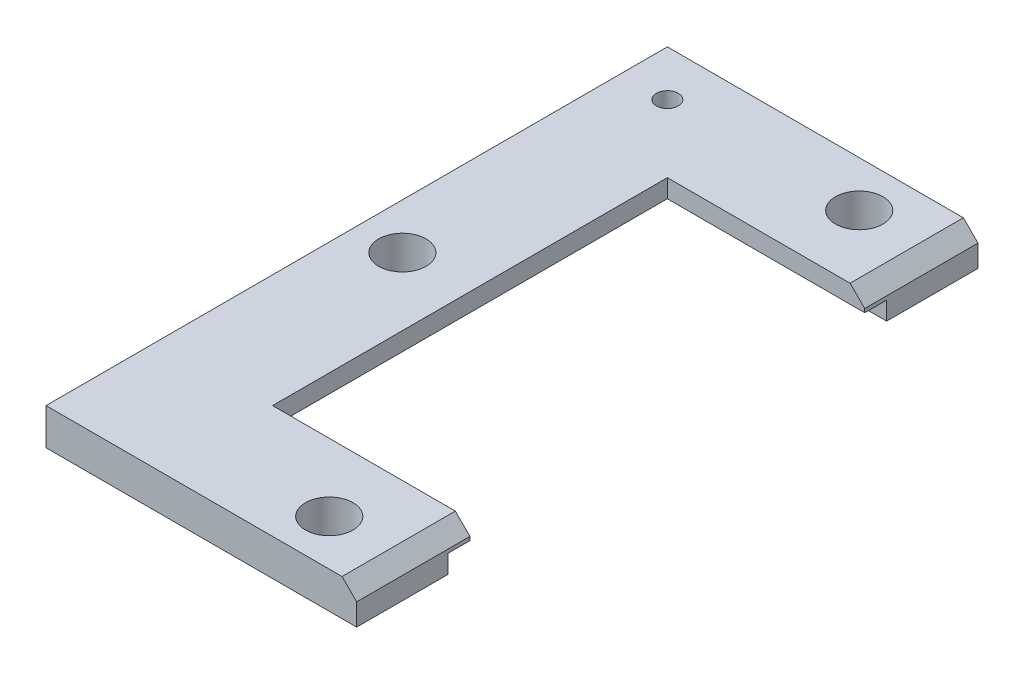
SolidWorks part; units mm, degrees
material "Plain Carbon Steel"
ref_plane "Front Plane" through (0, 0, 0) normal (0, 0, 1) x (1, 0, 0)
ref_plane "Top Plane" through (0, 0, 0) normal (0, 1, 0) x (1, 0, 0)
ref_plane "Right Plane" through (0, 0, 0) normal (1, 0, 0) x (0, 0, -1)
sketch "Sketch1" plane through (0, 0, 0) normal (0, 1, 0) x (1, 0, 0)
  line L0 (-133.1766, -85) -> (-133.1766, -54)
  line L1 (-218.1766, 85) -> (-133.1766, 85)
  line L2 (-218.1766, 85) -> (-218.1766, -85)
  line L3 (-218.1766, -85) -> (-133.1766, -85)
  line L5 (-133.1766, 54) -> (-133.1766, 85)
  line L7 (-187.1766, 54) -> (-133.1766, 54)
  line L8 (-187.1766, 54) -> (-187.1766, -54)
  line L9 (-187.1766, -54) -> (-133.1766, -54)
  point P0 (0, 0)
  point P6 (0, 0)
  dimension "D1" = 31
  dimension "D2" = 31
  dimension "D3" = 170
  dimension "D4" = 85
  dimension "D5" = 31
extrude "Boss-Extrude1" add sketch "Sketch1" along normal blind 10
sketch "Sketch2" plane through (0, 0, 0) normal (0, -1, 0) x (1, 0, 0)
  line L0 (-133.1766, 60) -> (-193.1766, 60)
  line L1 (-133.1766, 85) -> (-133.1766, 54) construction
  line L2 (-193.1766, 60) -> (-193.1766, -60)
  line L3 (-193.1766, -60) -> (-133.1766, -60)
  line L4 (-133.1766, -54) -> (-133.1766, -85) construction
  line L5 (-133.1766, -60) -> (-133.1766, -54)
  line L6 (-187.1766, -54) -> (-133.1766, -54) construction
  line L7 (-133.1766, -54) -> (-187.1766, -54)
  line L8 (-187.1766, -54) -> (-187.1766, 54)
  line L9 (-187.1766, 54) -> (-133.1766, 54)
  line L10 (-133.1766, 54) -> (-133.1766, 60)
  dimension "D1" = 6
  dimension "D2" = 6
  dimension "D3" = 6
extrude "Cut-Extrude1" cut sketch "Sketch2" against normal blind 5
chamfer "Chamfer1" distance 4 angle 45
sketch "Sketch3" plane through (0, 0, 0) normal (0, -1, 0) x (1, 0, 0)
  line L0 (-133.1766, -85) -> (-218.1766, -85) construction
  line L2 (-133.1766, -60) -> (-133.1766, -85) construction
  line L3 (-187.1766, 0) -> (-218.1766, 0) construction
  line L4 (-187.1766, -54) -> (-187.1766, 54) construction
  line L5 (-218.1766, -85) -> (-218.1766, 85) construction
  circle A0 centre (-153.1766, -72.5) radius 6.5
  circle A1 centre (-153.1766, 72.5) radius 6.5
  circle A2 centre (-205.6766, 0) radius 6.5
  dimension "D1" = 13
  dimension "D4" = 13
  dimension "D5" = 12.5
  dimension "D2" = 12.5
  dimension "D3" = 20
extrude "Cut-Extrude2" cut sketch "Sketch3" against normal through all
sketch "Sketch7" plane through (0, 0, 0) normal (0, -1, 0) x (1, 0, 0)
  line L0 (-218.1766, -85) -> (-218.1766, 85) construction
  line L1 (-133.1766, -85) -> (-218.1766, -85) construction
  circle A0 centre (-205.6766, -72.5) radius 3
  dimension "D1" = 6
  dimension "D2" = 12.5
  dimension "D3" = 12.5
extrude "Cut-Extrude3" cut sketch "Sketch7" against normal through all
